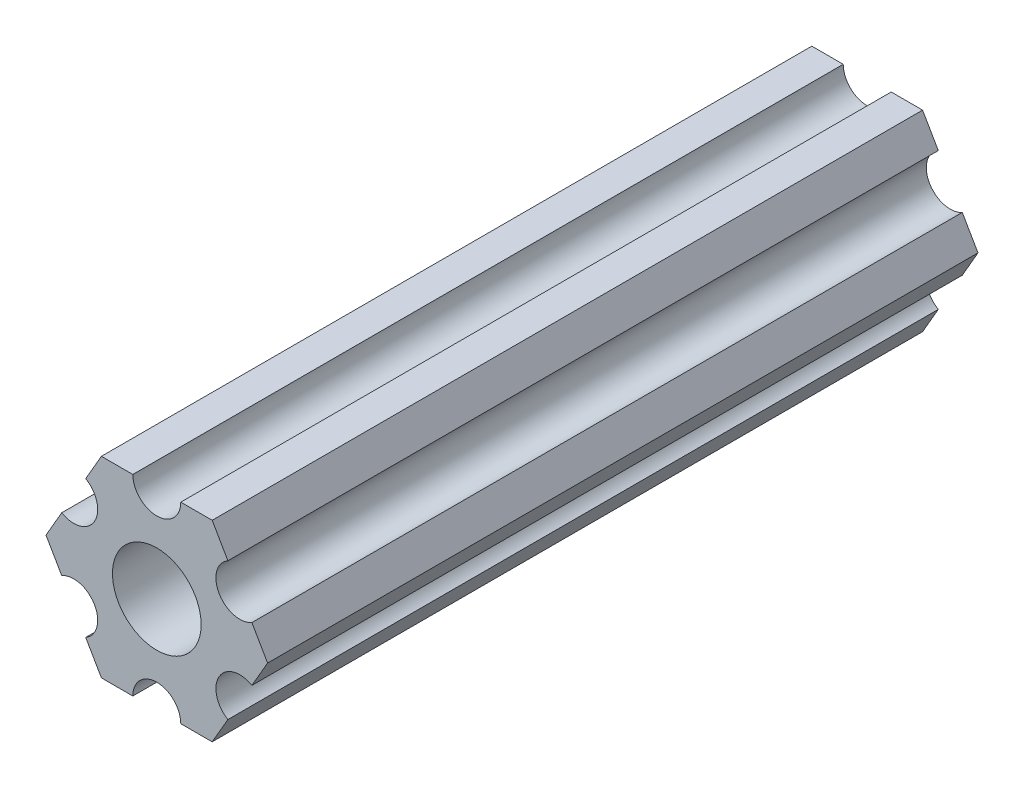
SolidWorks part; units mm, degrees
ref_plane "Front Plane" through (0, 0, 0) normal (0, 0, 1) x (1, 0, 0)
ref_plane "Top Plane" through (0, 0, 0) normal (0, 1, 0) x (1, 0, 0)
ref_plane "Right Plane" through (0, 0, 0) normal (1, 0, 0) x (0, 0, -1)
ref_plane "Plane1" through (0, 0, 0) normal (0, 0, -1) x (-1, 0, 0)
sketch "Sketch1" plane through (0, 0, 0) normal (0, 0, -1) x (-1, 0, 0)
  line L0 (-4.7055, -4.5498) -> (-3.6662, -6.35)
  line L1 (-3.6662, -6.35) -> (-1.5875, -6.35)
  line L2 (1.5875, -6.35) -> (3.6662, -6.35)
  line L3 (3.6662, -6.35) -> (4.7055, -4.5498)
  line L4 (6.293, -1.8002) -> (7.3323, 0)
  line L5 (7.3323, 0) -> (6.293, 1.8002)
  line L6 (4.7055, 4.5498) -> (3.6662, 6.35)
  line L7 (3.6662, 6.35) -> (1.5875, 6.35)
  line L8 (-1.5875, 6.35) -> (-3.6662, 6.35)
  line L9 (-3.6662, 6.35) -> (-4.7055, 4.5498)
  line L10 (-6.293, 1.8002) -> (-7.3323, 0)
  line L11 (-7.3323, 0) -> (-6.293, -1.8002)
  circle A0 centre (0, 0) radius 2.9337
  arc A1 (-6.293, -1.8002) -> (-4.7055, -4.5498) centre (-5.4993, -3.175) cw
  arc A2 (-1.5875, -6.35) -> (1.5875, -6.35) centre (0, -6.35) cw
  arc A3 (4.7055, -4.5498) -> (6.293, -1.8002) centre (5.4993, -3.175) cw
  arc A4 (6.293, 1.8002) -> (4.7055, 4.5498) centre (5.4993, 3.175) cw
  arc A5 (1.5875, 6.35) -> (-1.5875, 6.35) centre (0, 6.35) cw
  arc A6 (-4.7055, 4.5498) -> (-6.293, 1.8002) centre (-5.4993, 3.175) cw
  dimension "D1" = 5.8674
  dimension "D2" = 1.5875
  dimension "D3" = 5.4993
  dimension "D4" = 6.293
extrude "Boss-Extrude1" add sketch "Sketch1" against normal blind 47.0154
sketch "Sketch2" plane through (0, 0, 47.0154) normal (0, 0, 1) x (1, 0, 0)
  circle A0 centre (0, 0) radius 7.3323
sketch "Sketch3" plane through (0, 0, 47.0154) normal (0, 0, 1) x (1, 0, 0)
  line L0 (-1.5875, 6.35) -> (1.5875, 6.35)
  line L1 (-3.6662, 6.35) -> (-1.5875, 6.35) construction
  line L2 (1.5875, 6.35) -> (3.6662, 6.35) construction
  arc A0 (-1.5875, 6.35) -> (1.5875, 6.35) centre (0, 6.35) ccw construction
  arc A1 (-1.5875, 6.35) -> (1.5875, 6.35) centre (0, 6.35) ccw
